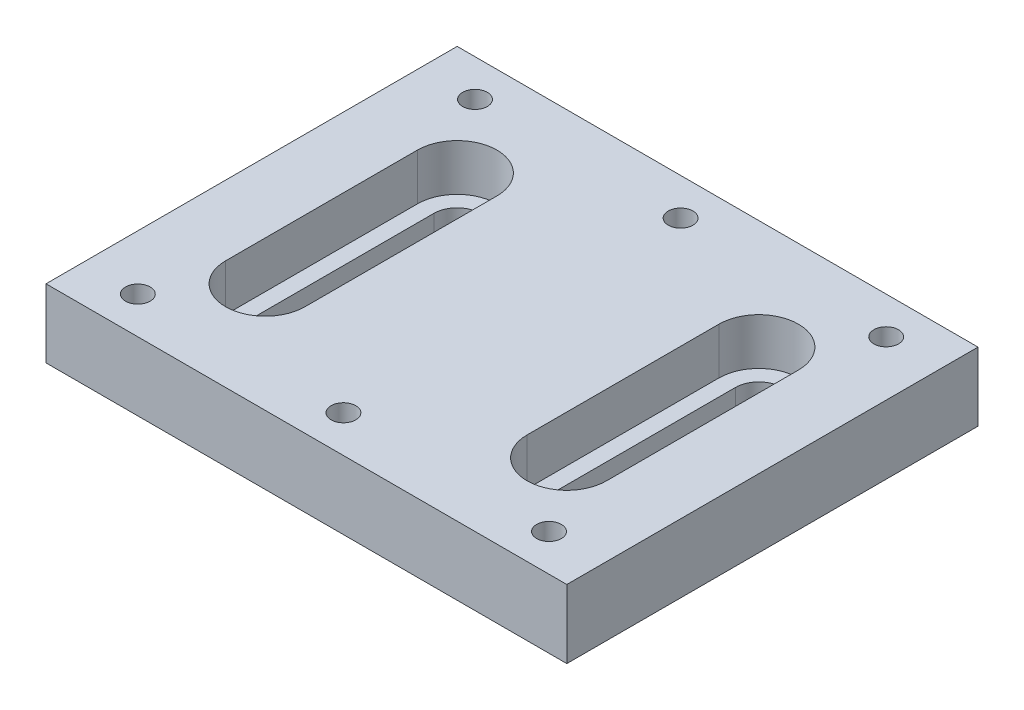
SolidWorks part; units mm, degrees
ref_plane "Front Plane" through (0, 0, 0) normal (0, 0, 1) x (1, 0, 0)
ref_plane "Top Plane" through (0, 0, 0) normal (0, 1, 0) x (1, 0, 0)
ref_plane "Right Plane" through (0, 0, 0) normal (1, 0, 0) x (0, 0, -1)
sketch "Sketch1" plane through (0, 0, 0) normal (0, 1, 0) x (1, 0, 0)
  line L1 (-24.13, 19.05) -> (24.13, 19.05)
  line L2 (-24.13, 19.05) -> (-24.13, -19.05)
  line L3 (-24.13, -19.05) -> (24.13, -19.05)
  line L4 (24.13, 19.05) -> (24.13, -19.05)
  line L5 (-24.13, 19.05) -> (24.13, -19.05) construction
  line L6 (-24.13, -19.05) -> (24.13, 19.05) construction
  point P0 (0, 0)
  dimension "D1" = 48.26
  dimension "D2" = 38.1
extrude "Boss-Extrude1" add sketch "Sketch1" against normal blind 6.35
sketch "Sketch2" plane through (0, 0, 0) normal (0, 1, 0) x (1, 0, 0)
  line L0 (-24.13, 19.05) -> (-24.13, -19.05) construction
  circle A0 centre (-13.97, 0) radius 3.683
  dimension "D1" = 7.366
  dimension "D2" = 10.16
extrude "Cut-Extrude1" cut sketch "Sketch2" against normal blind 4.318
sketch "Sketch3" plane through (0, -4.318, 0) normal (0, 1, 0) x (1, 0, 0)
  circle A0 centre (-13.97, 0) radius 2.159
  circle A1 centre (-13.97, 0) radius 3.683 construction
  dimension "D1" = 4.318
  dimension "D2" = 0
extrude "Cut-Extrude2" cut sketch "Sketch3" against normal blind 4.318
sketch "Sketch4" plane through (0, 0, 0) normal (0, 1, 0) x (1, 0, 0)
  line L0 (-24.13, 19.05) -> (-24.13, -19.05) construction
  circle A0 centre (-19.05, 15.621) radius 1.143
  circle A1 centre (-19.05, -15.621) radius 1.143
  dimension "D1" = 2.286
  dimension "D2" = 2.286
  dimension "D5" = 5.08
  dimension "D3" = 31.242
  dimension "D4" = 15.621
extrude "Cut-Extrude3" cut sketch "Sketch4" against normal blind 9.398
pattern_linear "LPattern1" count 3 spacing 19.05 along (1, 0, 0) of "Cut-Extrude3"
mirror "Mirror1" about plane through (0, 0, 0) normal (1, 0, 0) of "Cut-Extrude2", "Cut-Extrude1"
sketch "Sketch6" plane through (0, 0, 0) normal (0, 1, 0) x (1, 0, 0)
  line L0 (-13.97, -8.89) -> (-13.97, 8.89) construction
  line L1 (-17.653, -8.89) -> (-17.653, 8.89)
  line L2 (-10.287, -8.89) -> (-10.287, 8.89)
  arc A0 (-17.653, -8.89) -> (-10.287, -8.89) centre (-13.97, -8.89) ccw
  arc A1 (-10.287, 8.89) -> (-17.653, 8.89) centre (-13.97, 8.89) ccw
  point P2 (-13.97, 0)
  dimension "D1" = 3.683
  dimension "D2" = 17.78
extrude "Cut-Extrude7" cut sketch "Sketch6" against normal up to surface (4.318 mm away) up to face at (-13.97, -4.318, 2.159)
sketch "Sketch7" plane through (0, -4.318, 0) normal (0, 1, 0) x (1, 0, 0)
  line L0 (-13.97, -8.89) -> (-13.97, 8.89) construction
  line L1 (-16.129, -8.89) -> (-16.129, 8.89)
  line L2 (-11.811, -8.89) -> (-11.811, 8.89)
  arc A0 (-16.129, -8.89) -> (-11.811, -8.89) centre (-13.97, -8.89) ccw
  arc A1 (-11.811, 8.89) -> (-16.129, 8.89) centre (-13.97, 8.89) ccw
  circle A2 centre (-13.97, 0) radius 2.159 construction
  arc A3 (-10.287, 8.89) -> (-17.653, 8.89) centre (-13.97, 8.89) ccw construction
  point P2 (-13.97, 0)
  dimension "D2" = 0
  dimension "D1" = 2.159
extrude "Cut-Extrude8" cut sketch "Sketch7" against normal blind 10.16
mirror "Mirror2" about plane through (0, 0, 0) normal (1, 0, 0) of "Cut-Extrude8", "Cut-Extrude7"
